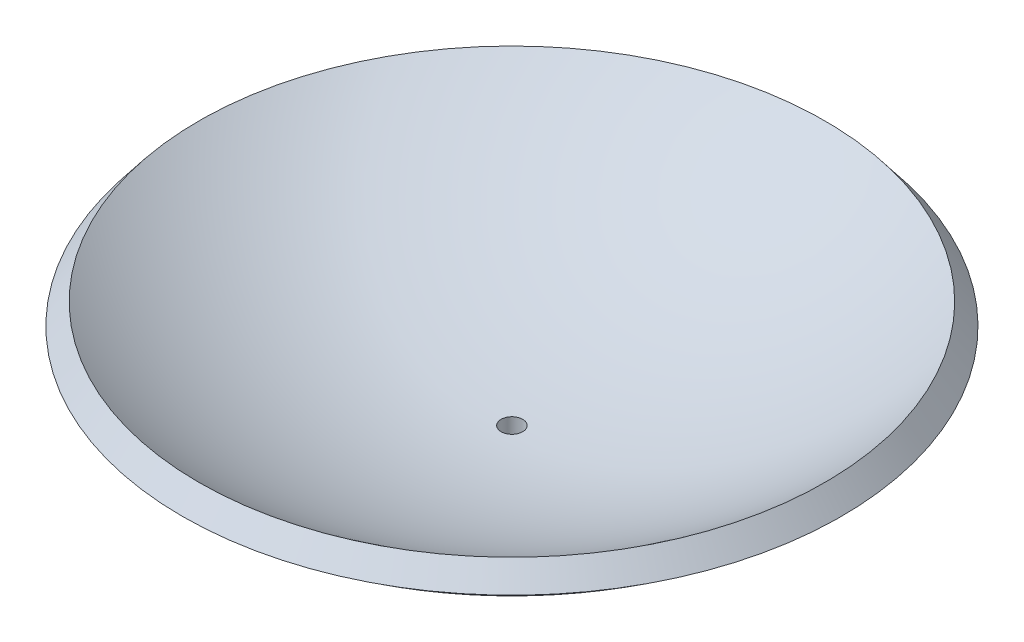
SolidWorks part; units mm, degrees
material "PET"
ref_plane "Front Plane" through (0, 0, 0) normal (0, 0, 1) x (1, 0, 0)
ref_plane "Top Plane" through (0, 0, 0) normal (0, 1, 0) x (1, 0, 0)
ref_plane "Right Plane" through (0, 0, 0) normal (1, 0, 0) x (0, 0, -1)
sketch "Sketch1" plane through (0, 0, 0) normal (0, 0, 1) x (1, 0, 0)
  line L0 (0, 0) -> (-12.7, 0)
  line L1 (-12.7, 0) -> (-12.7, 6.35)
  line L2 (-77.9506, 32.4502) -> (-74.0531, 37.4634)
  line L3 (0, 25.8108) -> (0, -14.8756) construction
  line L4 (0, 0) -> (0, 12.0634)
  arc A0 (-12.7, 6.35) -> (-77.9506, 32.4502) centre (0, 132.7134) cw
  arc A1 (-74.0531, 37.4634) -> (0, 12.0634) centre (0, 132.7134) ccw
  point P3 (0, 0)
  point P9 (-78.5941, 32.9539)
  point P10 (-80.9536, 34.8588)
  dimension "D1" = 120.65
  dimension "D3" = 6.35
  dimension "D2" = 6.35
  dimension "D4" = 12.7
  dimension "D5" = 25.4
revolve "Revolve1" add sketch "Sketch1" angle 360 about L3
hole_wizard "1/4-20 Tapped Hole1" positions "Sketch2" profile "Sketch3" tap size "1/4-20" standard "ANSI Inch"
sketch "Sketch2" plane through (0, 0, 0) normal (0, -1, 0) x (-1, 0, 0)
  point P0 (0, 0)
sketch "Sketch3" plane through (0, 0, 0) normal (1, 0, 0) x (0, 0, -1)
  line L0 (0, 0) -> (0, 14.2338)
  line L1 (0, 14.2338) -> (2.5527, 12.7)
  line L2 (2.5527, 12.7) -> (2.5527, 0)
  line L5 (2.5527, 0) -> (0, 0)
  line L10 (0, 14.2338) -> (-2.5527, 12.7) construction
  line L11 (0, -6.35) -> (0, 107.95) construction
  dimension "Tap Drill Dia." = 5.1054
  dimension "Tap Drill Depth" = 12.7
  dimension "Drill Angle" = 118
cosmetic thread "Hole Thread1" parameters "D1"=12.7, "D2"=6.35
